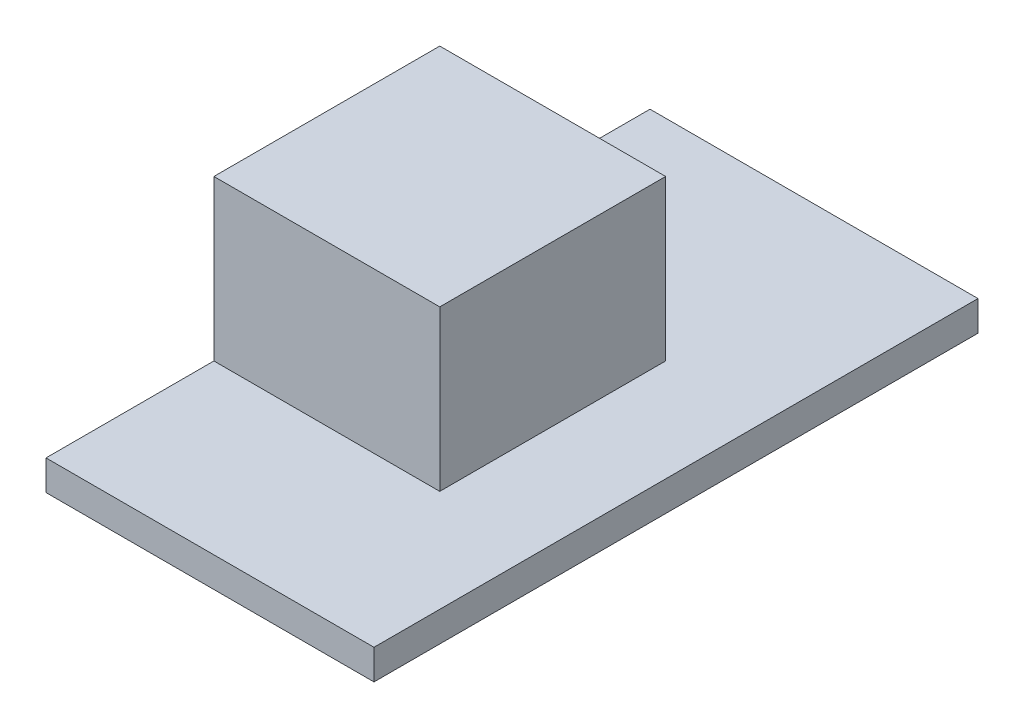
SolidWorks part; units mm, degrees
ref_plane "Front Plane" through (0, 0, 0) normal (0, 0, 1) x (1, 0, 0)
ref_plane "Top Plane" through (0, 0, 0) normal (0, 1, 0) x (1, 0, 0)
ref_plane "Right Plane" through (0, 0, 0) normal (1, 0, 0) x (0, 0, -1)
sketch "Sketch1" plane through (0, 0, 0) normal (0, 1, 0) x (1, 0, 0)
  line L1 (-5.46, 10.055) -> (5.46, 10.055)
  line L2 (-5.46, 10.055) -> (-5.46, -10.055)
  line L3 (-5.46, -10.055) -> (5.46, -10.055)
  line L4 (5.46, 10.055) -> (5.46, -10.055)
  line L5 (-5.46, 10.055) -> (5.46, -10.055) construction
  line L6 (-5.46, -10.055) -> (5.46, 10.055) construction
  point P0 (0, 0)
  dimension "D1" = 10.92
  dimension "D2" = 20.11
extrude "Boss-Extrude1" add sketch "Sketch1" along normal blind 1
sketch "Sketch2" plane through (0, 1, 0) normal (0, 1, 0) x (1, 0, 0)
  line L0 (-5.46, 10.055) -> (-5.46, 3.055) construction
  line L1 (-5.46, 10.055) -> (-5.46, -10.055) construction
  line L2 (-5.46, 3.055) -> (2.06, 3.055)
  line L3 (2.06, 3.055) -> (2.06, -4.465)
  line L4 (2.06, -4.465) -> (-5.46, -4.465)
  line L5 (-5.46, -4.465) -> (-5.46, 3.055)
extrude "Boss-Extrude2" add sketch "Sketch2" along normal blind 5.32
